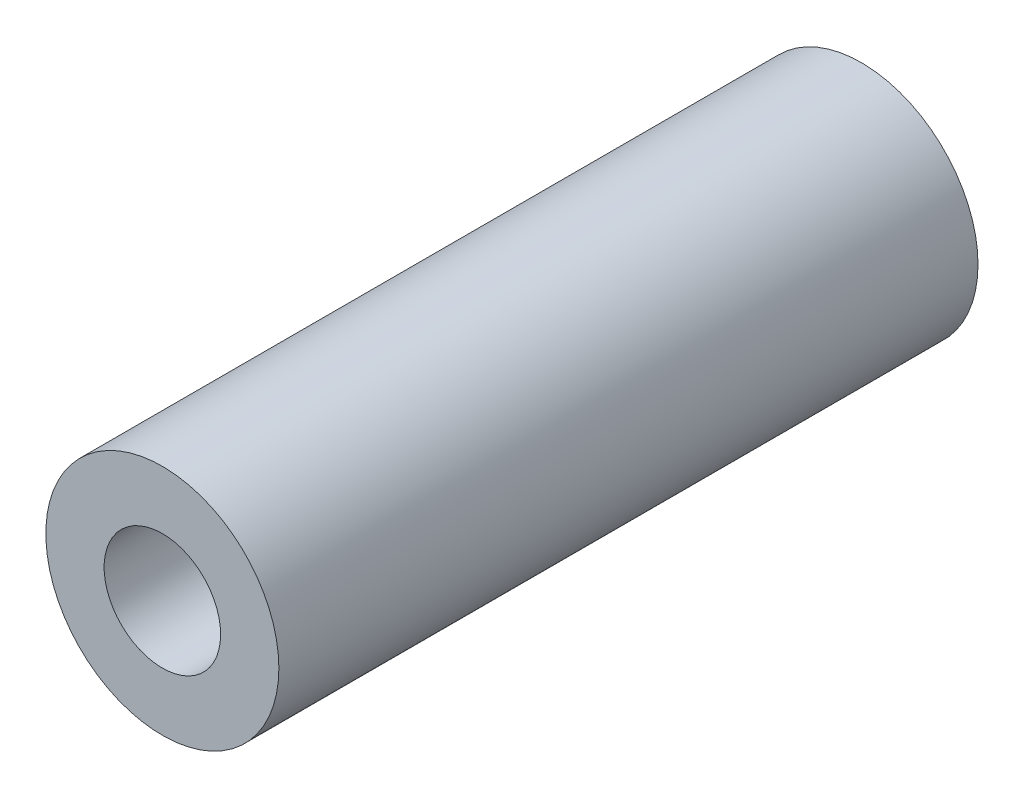
SolidWorks part; units mm, degrees
ref_plane "Front Plane" through (0, 0, 0) normal (0, 0, 1) x (1, 0, 0)
ref_plane "Top Plane" through (0, 0, 0) normal (0, 1, 0) x (1, 0, 0)
ref_plane "Right Plane" through (0, 0, 0) normal (1, 0, 0) x (0, 0, -1)
sketch "Sketch1" plane through (0, 0, 0) normal (0, 0, 1) x (1, 0, 0)
  circle A0 centre (0, 0) radius 50
  circle A1 centre (0, 0) radius 25
extrude "Boss-Extrude1" add sketch "Sketch1" along normal blind 300
